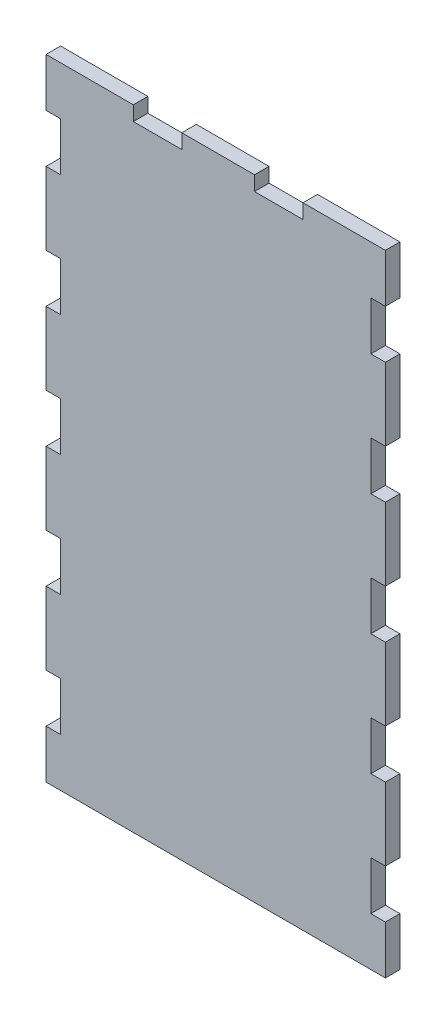
SolidWorks part; units mm, degrees
ref_plane "Plan de face" through (0, 0, 0) normal (0, 0, 1) x (1, 0, 0)
ref_plane "Plan de dessus" through (0, 0, 0) normal (0, 1, 0) x (1, 0, 0)
ref_plane "Plan de droite" through (0, 0, 0) normal (1, 0, 0) x (0, 0, -1)
sketch "Esquisse1" plane through (0, 0, 0) normal (0, 0, 1) x (1, 0, 0)
  line L0 (31.516, -1.2122) -> (14.516, -1.2122)
  line L1 (-38.484, -1.2122) -> (-38.484, -11.2122)
  line L2 (-38.484, -11.2122) -> (-35.484, -11.2122)
  line L3 (-35.484, -11.2122) -> (-35.484, -21.2122)
  line L4 (-35.484, -21.2122) -> (-38.484, -21.2122)
  line L5 (-38.484, -21.2122) -> (-38.484, -36.2122)
  line L6 (-38.484, -36.2122) -> (-35.484, -36.2122)
  line L7 (-35.484, -36.2122) -> (-35.484, -46.2122)
  line L8 (-35.484, -46.2122) -> (-38.484, -46.2122)
  line L9 (-38.484, -46.2122) -> (-38.484, -61.2122)
  line L10 (-38.484, -61.2122) -> (-35.484, -61.2122)
  line L11 (-35.484, -61.2122) -> (-35.484, -71.2122)
  line L12 (-35.484, -71.2122) -> (-38.484, -71.2122)
  line L13 (-38.484, -71.2122) -> (-38.484, -86.2122)
  line L14 (-38.484, -86.2122) -> (-35.484, -86.2122)
  line L15 (-35.484, -86.2122) -> (-35.484, -96.2122)
  line L16 (-38.484, -96.2122) -> (-35.484, -96.2122)
  line L17 (-38.484, -96.2122) -> (-38.484, -111.2122)
  line L18 (-38.484, -111.2122) -> (-35.484, -111.2122)
  line L19 (-35.484, -111.2122) -> (-35.484, -121.2122)
  line L20 (-35.484, -121.2122) -> (-38.484, -121.2122)
  line L21 (-38.484, -121.2122) -> (-38.484, -131.2122)
  line L22 (-38.484, -131.2122) -> (31.516, -131.2122)
  line L23 (-3.484, -1.2122) -> (-3.484, -155.474) construction
  line L24 (31.516, -121.2122) -> (31.516, -131.2122)
  line L25 (28.516, -121.2122) -> (31.516, -121.2122)
  line L26 (28.516, -111.2122) -> (28.516, -121.2122)
  line L27 (31.516, -111.2122) -> (28.516, -111.2122)
  line L28 (31.516, -96.2122) -> (31.516, -111.2122)
  line L29 (31.516, -96.2122) -> (28.516, -96.2122)
  line L30 (28.516, -86.2122) -> (28.516, -96.2122)
  line L31 (31.516, -86.2122) -> (28.516, -86.2122)
  line L32 (31.516, -71.2122) -> (31.516, -86.2122)
  line L33 (28.516, -71.2122) -> (31.516, -71.2122)
  line L34 (28.516, -61.2122) -> (28.516, -71.2122)
  line L35 (31.516, -61.2122) -> (28.516, -61.2122)
  line L36 (31.516, -46.2122) -> (31.516, -61.2122)
  line L37 (28.516, -46.2122) -> (31.516, -46.2122)
  line L38 (28.516, -36.2122) -> (28.516, -46.2122)
  line L39 (31.516, -36.2122) -> (28.516, -36.2122)
  line L40 (31.516, -21.2122) -> (31.516, -36.2122)
  line L41 (28.516, -21.2122) -> (31.516, -21.2122)
  line L42 (28.516, -11.2122) -> (28.516, -21.2122)
  line L43 (31.516, -11.2122) -> (28.516, -11.2122)
  line L44 (31.516, -1.2122) -> (31.516, -11.2122)
  line L45 (-20.484, -1.2122) -> (-20.484, -4.2122)
  line L46 (-20.484, -4.2122) -> (-10.484, -4.2122)
  line L47 (-10.484, -4.2122) -> (-10.484, -1.2122)
  line L48 (4.516, -1.2122) -> (4.516, -4.2122)
  line L49 (4.516, -4.2122) -> (14.516, -4.2122)
  line L50 (14.516, -4.2122) -> (14.516, -1.2122)
  line L51 (-20.484, -1.2122) -> (-38.484, -1.2122)
  line L52 (4.516, -1.2122) -> (-10.484, -1.2122)
  point P27 (-3.484, -131.2122)
  dimension "D1" = 70
  dimension "D2" = 10
  dimension "D3" = 10
  dimension "D4" = 15
  dimension "D5" = 10
  dimension "D6" = 15
  dimension "D7" = 10
  dimension "D8" = 15
  dimension "D9" = 10
  dimension "D10" = 15
  dimension "D11" = 10
  dimension "D12" = 10
  dimension "D13" = 3
  dimension "D14" = 10
  dimension "D15" = 10
  dimension "D16" = 15
  dimension "D17" = 18
  dimension "D18" = 3
  dimension "D19" = 3
extrude "Boss.-Extru.1" add sketch "Esquisse1" along normal blind 3
